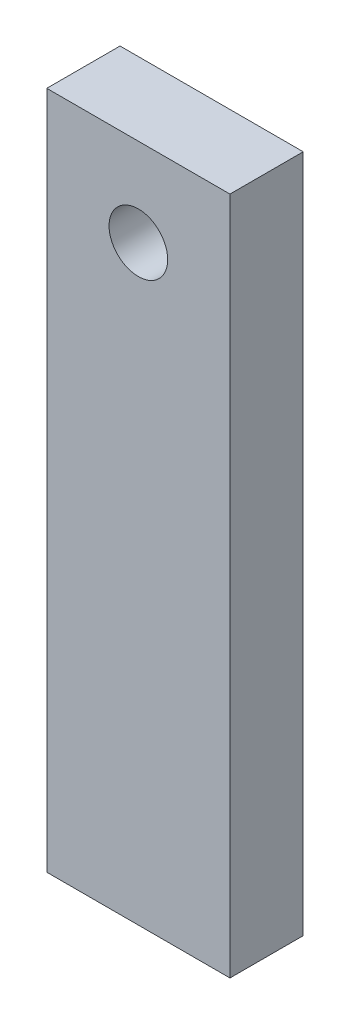
SolidWorks part; units mm, degrees
ref_plane "Front Plane" through (0, 0, 0) normal (0, 0, 1) x (1, 0, 0)
ref_plane "Top Plane" through (0, 0, 0) normal (0, 1, 0) x (1, 0, 0)
ref_plane "Right Plane" through (0, 0, 0) normal (1, 0, 0) x (0, 0, -1)
sketch "Sketch1" plane through (0, 0, 0) normal (0, 0, 1) x (1, 0, 0)
  line L0 (-12.5, 34.3293) -> (12.5, 34.3293) construction
  line L1 (-12.5, 46.3293) -> (12.5, 46.3293)
  line L2 (-12.5, 46.3293) -> (-12.5, -46.3293)
  line L3 (-12.5, -46.3293) -> (12.5, -46.3293)
  line L4 (12.5, 46.3293) -> (12.5, -46.3293)
  line L5 (-12.5, 46.3293) -> (12.5, -46.3293) construction
  line L6 (-12.5, -46.3293) -> (12.5, 46.3293) construction
  circle A0 centre (0, 34.3293) radius 4
  circle A1 centre (0, 34.3293) radius 28.5 construction
  point P0 (0, 0)
  point P6 (12.5, 0)
  point P7 (0, 0)
  dimension "D3" = 8
  dimension "D5" = 57
  dimension "D1" = 80.6586
  dimension "D2" = 25
  dimension "D4" = 12
extrude "Boss-Extrude1" add sketch "Sketch1" along normal blind 10
